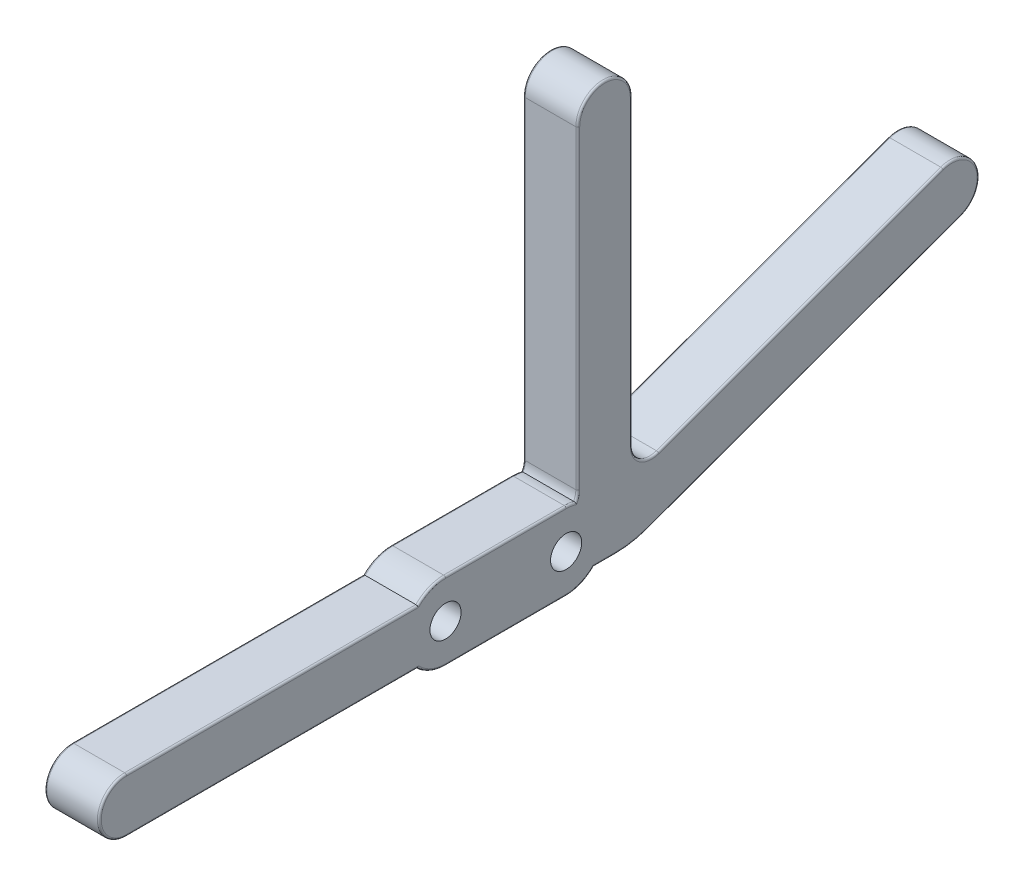
SolidWorks part; units mm, degrees
ref_plane "Front Plane" through (0, 0, 0) normal (0, 0, 1) x (1, 0, 0)
ref_plane "Top Plane" through (0, 0, 0) normal (0, 1, 0) x (1, 0, 0)
ref_plane "Right Plane" through (0, 0, 0) normal (1, 0, 0) x (0, 0, -1)
sketch "Sketch1" plane through (0, 0, 0) normal (1, 0, 0) x (0, 0, -1)
  line L0 (-58, 0) -> (-2.5, 0)
  line L1 (0, 2.5) -> (0, 42.9015)
  line L2 (7, 42.9015) -> (7, 4.0196)
  line L3 (10.3551, 1.6704) -> (46.892, 14.9688)
  line L4 (49.2862, 8.3909) -> (8.9883, -6.2763)
  line L5 (4.8841, -7) -> (-58, -7)
  line L6 (46.892, 14.9688) -> (49.2862, 8.3909) construction
  line L7 (0, 42.9015) -> (7, 42.9015) construction
  line L8 (-58, 0) -> (-58, -7) construction
  arc A0 (0, 42.9015) -> (7, 42.9015) centre (3.5, 42.9015) cw
  arc A1 (46.892, 14.9688) -> (49.2862, 8.3909) centre (48.0891, 11.6798) cw
  arc A2 (-58, 0) -> (-58, -7) centre (-58, -3.5) ccw
  arc A3 (7, 4.0196) -> (10.3551, 1.6704) centre (9.5, 4.0196) ccw
  arc A4 (-2.5, 0) -> (0, 2.5) centre (-2.5, 2.5) ccw
  arc A5 (8.9883, -6.2763) -> (4.8841, -7) centre (4.8841, 5) cw
  point P15 (7, 0.4492)
  point P18 (0, 0)
  point P21 (7, -7)
  dimension "D5" = 2.5
  dimension "D6" = 12
  dimension "D1" = 65
  dimension "D2" = 7
  dimension "D3" = 70
  dimension "D4" = 45
extrude "Boss-Extrude1" add sketch "Sketch1" along normal blind 7
sketch "Sketch2" plane through (7, 0, 0) normal (1, 0, 0) x (0, 0, -1)
  line L0 (3.5, 46.4015) -> (3.5, -7) construction
  line L1 (-58, -7) -> (4.8841, -7) construction
  line L2 (-17, -3.5) -> (-1.5, -3.5) construction
  line L3 (-17, 1.5) -> (-1.5, 1.5)
  line L4 (-17, -8.5) -> (-1.5, -8.5)
  line L5 (-9.25, 0) -> (-9.25, -7) construction
  line L6 (-2.5, 0) -> (-58, 0) construction
  arc A0 (7, 42.9015) -> (0, 42.9015) centre (3.5, 42.9015) ccw construction
  arc A1 (-17, 1.5) -> (-17, -8.5) centre (-17, -3.5) ccw
  arc A2 (-1.5, -8.5) -> (-1.5, 1.5) centre (-1.5, -3.5) ccw
  point P9 (-9.25, -3.5)
  dimension "D1" = 10
  dimension "D2" = 15.5
extrude "Boss-Extrude2" add sketch "Sketch2" against normal up to surface (7 mm away) up to face at (0, 8.3502, -1.3027)
fillet "Fillet1" radius 0.25 38 edges at (0, -7, -3.4774) (0, 1.9077, 0.0712) (0, 22.7007, 0) (0, 46.4015, -3.5) (0, 23.4605, -7) (0, 1.9717, -8.0661) (0, 8.3196, -28.6235) (0, 12.8769, -51.378) (0, 1.0573, -29.1372) (7, 1.9077, 0.0712) (7, 22.7007, 0) (7, 46.4015, -3.5) (7, 23.4605, -7) (7, 1.9717, -8.0661) (7, 8.3196, -28.6235) (7, 12.8769, -51.378) (7, 1.0573, -29.1372) (7, -6.8177, -6.9679) (7, -8.1098, -0.4365) (0, -8.1098, -0.4365) (0, -8.5, 9.25) (7, -8.5, 9.25) (7, 1.4621, 0.8857) (0, 1.4621, 0.8857) (0, 1.5, 9.25) (7, 1.5, 9.25) (0, -7, 39.2854) (0, -3.5, 61.5) (7, -7, 39.2854) (7, -3.5, 61.5) (0, -6.8177, -6.9679) (7, -7, -3.4774) (7, -8.1098, 18.9365) (0, -8.1098, 18.9365) (7, 1.1098, 18.9365) (0, 1.1098, 18.9365) (0, 0, 39.2854) (7, 0, 39.2854)
sketch "Sketch4" plane through (0, 0, 0) normal (1, 0, 0) x (0, 0, -1)
  line L0 (-17, 1.25) -> (-17, -8.25) construction
  line L1 (-1.5, 1.25) -> (-1.5, -8.25) construction
  circle A0 centre (-17, -3.5) radius 2
  circle A1 centre (-1.5, -3.5) radius 2
  dimension "D1" = 4
extrude "Cut-Extrude2" cut sketch "Sketch4" along normal up to surface (7 mm away) up to face at (7, 3.8694, 3.0844)
sketch "Sketch3" plane through (0, 0, 0) normal (1, 0, 0) x (0, 0, -1)
  line L2 (-58, 0) -> (-58, -7) construction
  line L3 (-58, -7) -> (-13.4293, -7) construction
  circle A3 centre (3.5, 42.9015) radius 1.125
  circle A4 centre (48.0891, 11.6798) radius 1.125
  circle A5 centre (-58, -3.5) radius 1.125
  arc A6 (-58, -7) -> (-58, 0) centre (-58, -3.5) ccw construction
  dimension "D2" = 2.25
extrude "Cut-Extrude1" cut sketch "Sketch3" along normal blind 5.5
